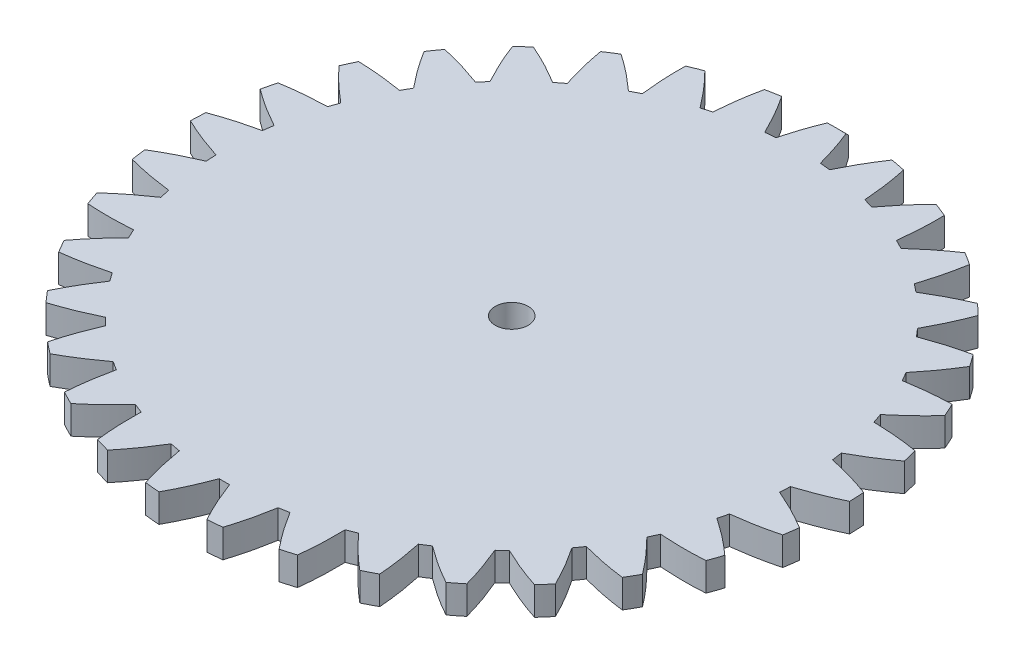
SolidWorks part; units mm, degrees
ref_plane "정면" through (0, 0, 0) normal (0, 0, 1) x (1, 0, 0)
ref_plane "윗면" through (0, 0, 0) normal (0, 1, 0) x (1, 0, 0)
ref_plane "우측면" through (0, 0, 0) normal (1, 0, 0) x (0, 0, -1)
sketch "스케치1" plane through (0, 0, 0) normal (0, 1, 0) x (1, 0, 0)
  circle A0 centre (0, 0) radius 33 construction
  circle A1 centre (0, 0) radius 30.5
  dimension "D1" = 66
  dimension "D2" = 2.5
extrude "보스-돌출2" add sketch "스케치1" along normal mid plane 3
sketch "스케치4" plane through (0, 1.5, 0) normal (0, 1, 0) x (1, 0, 0)
  line L0 (0, 0) -> (0, 50000) construction
  line L1 (-0.785, 0) -> (-0.785, 50000) construction
  line L2 (-1.57, 0) -> (-1.57, 50000) construction
  line L3 (-2.355, 0) -> (-2.355, 50000) construction
  circle A0 centre (0, 0) radius 33 construction
  arc A1 (0.785, 34.9912) -> (-0.785, 34.9912) centre (0, 0) ccw
  circle A2 centre (0, 0) radius 30.5
  arc A3 (-2.355, -34.9207) -> (0, -35) centre (0, 0) ccw
  circle A4 centre (0, 0) radius 35 construction
  spline S0 degree 2 poles (-2.355, 30.4089) (-1.7325, 32.7564) (-0.785, 34.9912) knots 0 0 0 1 1 1
  spline S1 degree 2 poles (2.355, 30.4089) (1.7325, 32.7564) (0.785, 34.9912) knots 0 0 0 1 1 1
  point P20 (35, 0)
  dimension "D1" = 66
  dimension "D2" = 2
  dimension "D3" = 0.785
  dimension "D4" = 0.785
  dimension "D5" = 0.785
extrude "보스-돌출3" add sketch "스케치4" against normal blind 3 contours A2 S1 A1 S0
chamfer "모따기2" distance 0.5 angle 45 2 edges at (0, 1.5, -35) (0, -1.5, -35)
pattern_circular "원형 패턴1" count 33 over 360 about axis through (0, 1.5, 0) along (0, -1, 0) of "보스-돌출3"
sketch "스케치5" plane through (0, 1.5, 0) normal (0, 1, 0) x (1, 0, 0)
  circle A0 centre (0, 0) radius 1.75
  dimension "D1" = 3.5
extrude "컷-돌출1" cut sketch "스케치5" against normal through all
